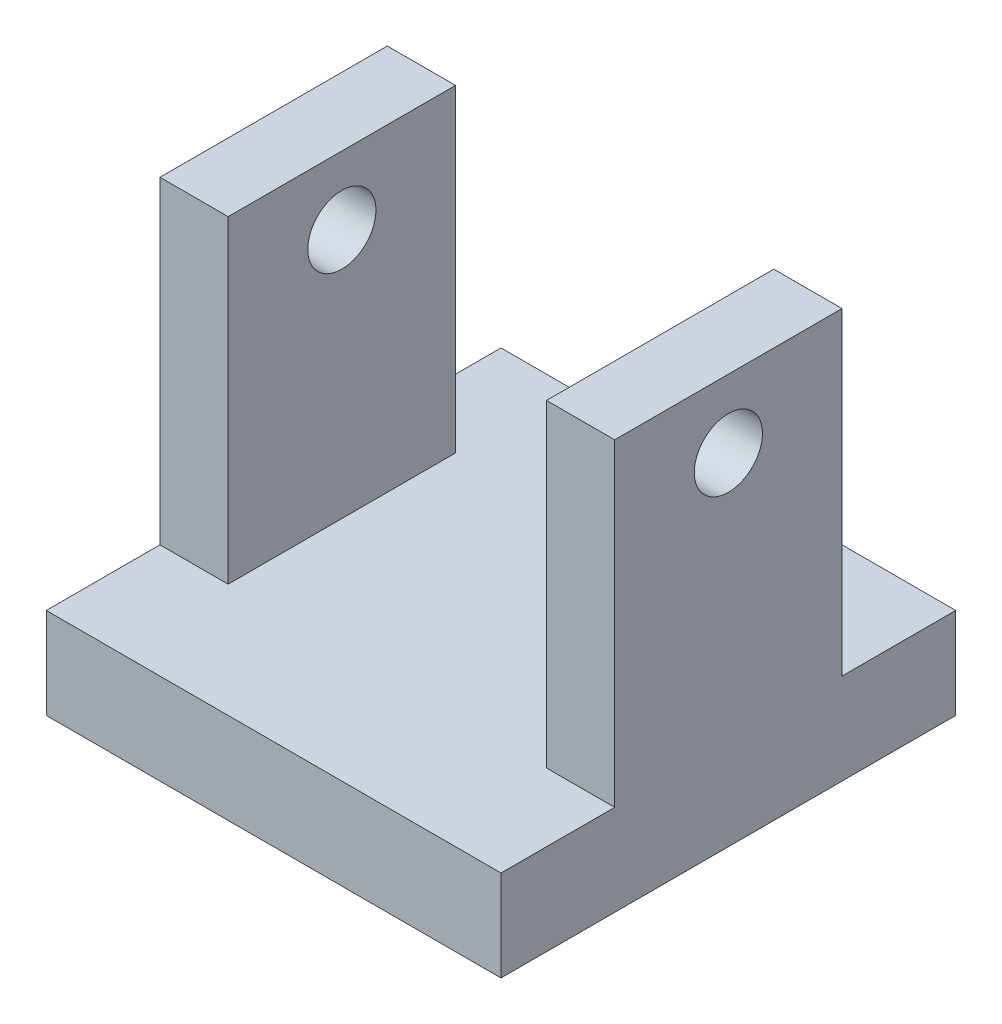
SolidWorks part; units mm, degrees
ref_plane "前视基准面" through (0, 0, 0) normal (0, 0, 1) x (1, 0, 0)
ref_plane "上视基准面" through (0, 0, 0) normal (0, 1, 0) x (1, 0, 0)
ref_plane "右视基准面" through (0, 0, 0) normal (1, 0, 0) x (0, 0, -1)
sketch "Sketch2" plane through (0, 0, 0) normal (0, 1, 0) x (1, 0, 0)
  line L1 (0, 0) -> (50, 0)
  line L2 (0, 0) -> (0, 50)
  line L3 (0, 50) -> (50, 50)
  line L4 (50, 0) -> (50, 50)
  dimension "D1" = 50
  dimension "D2" = 50
extrude "Boss-Extrude1" add sketch "Sketch2" along normal blind 10
sketch "Sketch3" plane through (0, 10, 0) normal (0, 1, 0) x (1, 0, 0)
  line L0 (0, 25) -> (50, 25) construction
  line L1 (0, 50) -> (0, 0) construction
  line L2 (50, 0) -> (50, 50) construction
  line L4 (0, 37.5) -> (7.5, 37.5)
  line L5 (0, 37.5) -> (0, 12.5)
  line L6 (0, 12.5) -> (7.5, 12.5)
  line L7 (7.5, 37.5) -> (7.5, 12.5)
  line L8 (50, 37.5) -> (42.5, 37.5)
  line L9 (50, 37.5) -> (50, 12.5)
  line L10 (50, 12.5) -> (42.5, 12.5)
  line L11 (42.5, 37.5) -> (42.5, 12.5)
  point P14 (0, 25)
  point P15 (50, 25)
  dimension "D1" = 25
  dimension "D2" = 25
  dimension "D3" = 7.5
  dimension "D4" = 7.5
extrude "Boss-Extrude2" add sketch "Sketch3" along normal blind 35
sketch "Sketch4" plane through (50, 0, 0) normal (1, 0, 0) x (0, 0, -1)
  line L0 (12.5, 45) -> (37.5, 45) construction
  line L2 (12.5, 45) -> (12.5, 10) construction
  circle A0 centre (25, 37.5) radius 3.75
  point P6 (37.5, 36.4189)
  point P7 (22.454, 37.0462)
  dimension "D1" = 7.5
  dimension "D2" = 7.5
  dimension "D3" = 12.5
extrude "Cut-Extrude1" cut sketch "Sketch4" against normal up to surface (50 mm away) up to face at (0, 16.25, -25)
